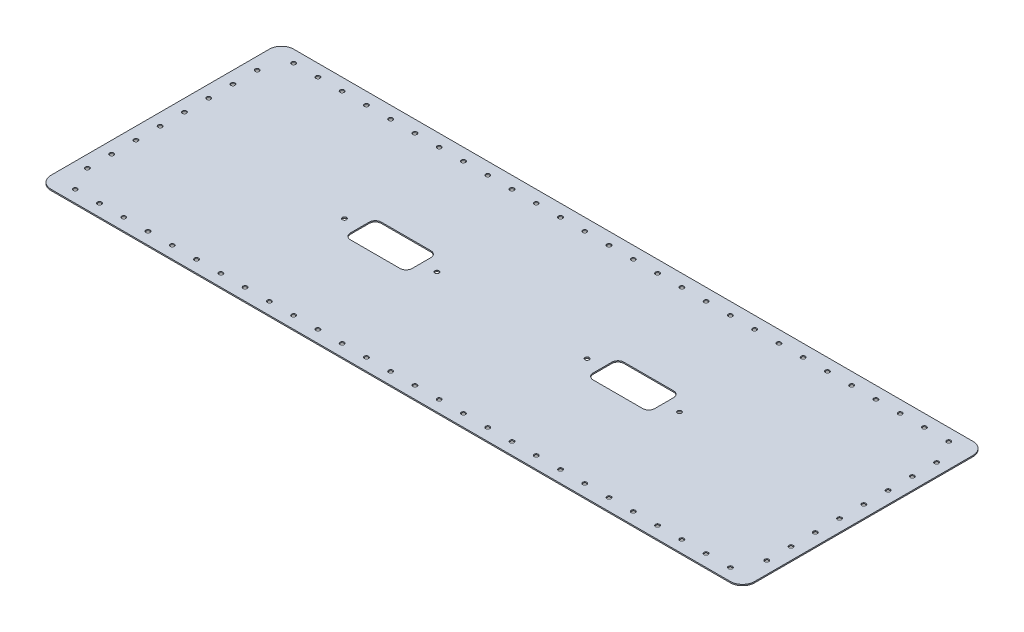
SolidWorks part; units mm, degrees
material "3003-H12"
ref_plane "Front Plane" through (0, 0, 0) normal (0, 0, 1) x (1, 0, 0)
ref_plane "Top Plane" through (0, 0, 0) normal (0, 1, 0) x (1, 0, 0)
ref_plane "Right Plane" through (0, 0, 0) normal (1, 0, 0) x (0, 0, -1)
sketch "Sketch1" plane through (0, 0, 0) normal (0, 1, 0) x (1, 0, 0)
  line L1 (-290, 100) -> (290, 100)
  line L2 (-290, 100) -> (-290, -100)
  line L3 (-290, -100) -> (290, -100)
  line L4 (290, 100) -> (290, -100)
  line L5 (-290, 100) -> (290, -100) construction
  line L6 (-290, -100) -> (290, 100) construction
  point P0 (0, 0)
  dimension "D1" = 580
  dimension "D2" = 200
extrude "Boss-Extrude1" add sketch "Sketch1" along normal blind 1
fillet "Fillet1" radius 10 4 edges at (-290, 0.5, 100) (290, 0.5, 100) (290, 0.5, -100) (-290, 0.5, -100)
hole_wizard "M3 Clearance Hole1" positions "Sketch2" profile "Sketch3" hole size "M3" standard "ANSI Metric" end condition through all
sketch "Sketch2" plane through (0, 1, 0) normal (0, 1, 0) x (1, 0, 0)
  line L0 (280, 100) -> (-280, 100) construction
  line L1 (290, -90) -> (290, 90) construction
  line L2 (-0.55, 0) -> (0.55, 0) construction
  line L3 (0, -0.55) -> (0, 0.55) construction
  point P1 (280, 70)
  point P3 (270, 90)
  point P17 (250, 90)
  point P18 (230, 90)
  point P19 (210, 90)
  point P20 (190, 90)
  point P21 (170, 90)
  point P22 (150, 90)
  point P23 (130, 90)
  point P24 (110, 90)
  point P25 (90, 90)
  point P26 (70, 90)
  point P27 (50, 90)
  point P28 (30, 90)
  point P29 (10, 90)
  point P30 (-10, 90)
  point P31 (-30, 90)
  point P32 (-50, 90)
  point P33 (-70, 90)
  point P34 (-90, 90)
  point P35 (-110, 90)
  point P36 (-130, 90)
  point P37 (-150, 90)
  point P38 (-170, 90)
  point P39 (-190, 90)
  point P40 (-210, 90)
  point P41 (-230, 90)
  point P42 (-250, 90)
  point P43 (-270, 90)
  point P51 (280, 50.003)
  point P52 (280, 30.0061)
  point P53 (280, 10.0091)
  point P54 (280, -9.9878)
  point P55 (280, -29.9848)
  point P56 (280, -49.9817)
  point P57 (280, -69.9787)
  point P60 (270, -90)
  point P61 (250, -90)
  point P62 (230, -90)
  point P63 (210, -90)
  point P64 (190, -90)
  point P65 (170, -90)
  point P66 (150, -90)
  point P67 (130, -90)
  point P68 (110, -90)
  point P69 (90, -90)
  point P70 (70, -90)
  point P71 (50, -90)
  point P72 (30, -90)
  point P73 (10, -90)
  point P74 (-10, -90)
  point P75 (-30, -90)
  point P76 (-50, -90)
  point P77 (-70, -90)
  point P78 (-90, -90)
  point P79 (-110, -90)
  point P80 (-130, -90)
  point P81 (-150, -90)
  point P82 (-170, -90)
  point P83 (-190, -90)
  point P84 (-210, -90)
  point P85 (-230, -90)
  point P86 (-250, -90)
  point P87 (-270, -90)
  point P90 (-280, 70)
  point P91 (-280, 50.003)
  point P92 (-280, 30.0061)
  point P93 (-280, 10.0091)
  point P94 (-280, -9.9878)
  point P95 (-280, -29.9848)
  point P96 (-280, -49.9817)
  point P97 (-280, -69.9787)
  dimension "D1" = 30
  dimension "D2" = 10
  dimension "D3" = 20
  dimension "D4" = 10
  dimension "D6" = 20
  dimension "D8" = 19.997
  dimension "D5" = 28
  dimension "D7" = 8
sketch "Sketch3" plane through (280, 1, -70) normal (1, 0, 0) x (0, 0, 1)
  line L0 (0, 0) -> (0, 1)
  line L1 (0, 1) -> (1.7, 1)
  line L2 (1.7, 1) -> (1.7, 0.025)
  line L3 (1.7, 0.025) -> (1.725, 0)
  line L5 (1.725, 0) -> (0, 0)
  line L6 (-1.7, 0.025) -> (-1.725, 0) construction
  line L11 (0, -6.35) -> (0, 107.95) construction
  dimension "Thru Hole Dia." = 3.4
  dimension "Thru Hole Depth" = 1
  dimension "Near C'Sink Dia." = 3.45
  dimension "Near C'Sink Angle" = 90
sketch "Sketch4" plane through (0, 1, 0) normal (0, 1, 0) x (1, 0, 0)
  line L0 (0, 0) -> (-100, 0) construction
  line L1 (-125.4, 12.7) -> (-74.6, 12.7)
  line L2 (-125.4, 12.7) -> (-125.4, -12.7)
  line L3 (-125.4, -12.7) -> (-74.6, -12.7)
  line L4 (-74.6, 12.7) -> (-74.6, -12.7)
  line L5 (-125.4, 12.7) -> (-74.6, -12.7) construction
  line L6 (-125.4, -12.7) -> (-74.6, 12.7) construction
  line L7 (0, -0.55) -> (0, 0.55) construction
  line L8 (74.6, 12.7) -> (74.6, -12.7)
  line L9 (125.4, -12.7) -> (74.6, -12.7)
  line L10 (125.4, 12.7) -> (125.4, -12.7)
  line L11 (125.4, 12.7) -> (74.6, 12.7)
  point P0 (-100, 0)
  dimension "D1" = 25.4
  dimension "D2" = 50.8
  dimension "D3" = 100
extrude "Cut-Extrude1" cut sketch "Sketch4" against normal blind 10
fillet "Fillet2" radius 5 8 edges at (74.6, 0.5, -12.7) (125.4, 0.5, -12.7) (125.4, 0.5, 12.7) (74.6, 0.5, 12.7) (-125.4, 0.5, 12.7) (-74.6, 0.5, 12.7) (-74.6, 0.5, -12.7) (-125.4, 0.5, -12.7)
hole_wizard "M3 Clearance Hole4" positions "Sketch5" profile "Sketch6" hole size "M3" standard "ANSI Metric" end condition through all
sketch "Sketch5" plane through (0, 1, 0) normal (0, 1, 0) x (1, 0, 0)
  line L0 (-61.9, 0) -> (-138.1, 0)
  line L2 (-100, 12.7) -> (-100, 0) construction
  line L3 (-79.6, 12.7) -> (-120.4, 12.7) construction
  line L5 (0, -0.55) -> (0, 0.55) construction
  line L6 (61.9, 0) -> (138.1, 0)
  point P1 (-61.9, 0)
  point P2 (-138.1, 0)
  point P14 (61.9, 0)
  point P15 (138.1, 0)
  dimension "D1" = 76.2
sketch "Sketch6" plane through (-61.9, 1, 0) normal (1, 0, 0) x (0, 0, 1)
  line L0 (0, 0) -> (0, 1)
  line L1 (0, 1) -> (1.7, 1)
  line L2 (1.7, 1) -> (1.7, 0.025)
  line L3 (1.7, 0.025) -> (1.725, 0)
  line L5 (1.725, 0) -> (0, 0)
  line L6 (-1.7, 0.025) -> (-1.725, 0) construction
  line L11 (0, -6.35) -> (0, 107.95) construction
  dimension "Thru Hole Dia." = 3.4
  dimension "Thru Hole Depth" = 1
  dimension "Near C'Sink Dia." = 3.45
  dimension "Near C'Sink Angle" = 90
